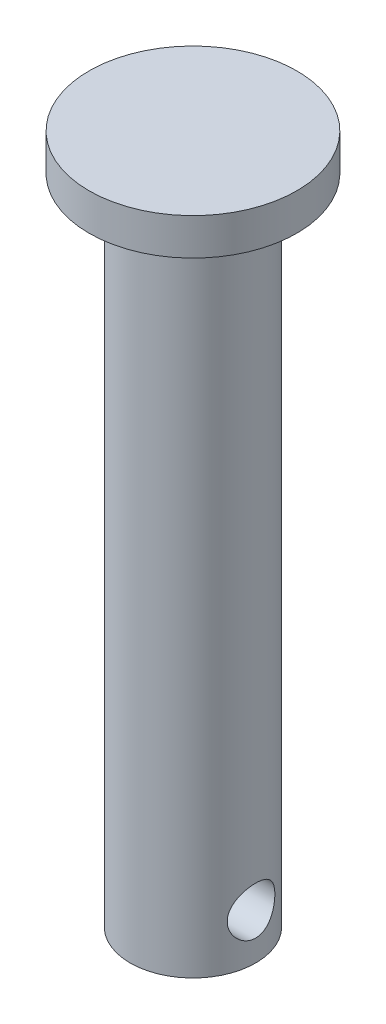
SolidWorks part; units mm, degrees
ref_plane "Front Plane" through (0, 0, 0) normal (0, 0, 1) x (1, 0, 0)
ref_plane "Top Plane" through (0, 0, 0) normal (0, 1, 0) x (1, 0, 0)
ref_plane "Right Plane" through (0, 0, 0) normal (1, 0, 0) x (0, 0, -1)
sketch "Sketch1" plane through (0, 0, 0) normal (0, 1, 0) x (1, 0, 0)
  circle A0 centre (0, 0) radius 2.9
  dimension "D1" = 5.8
extrude "Boss-Extrude1" add sketch "Sketch1" against normal blind 30.15
sketch "Sketch2" plane through (0, 0, 0) normal (0, 1, 0) x (1, 0, 0)
  circle A0 centre (0, 0) radius 4.8
  dimension "D1" = 9.6
extrude "Boss-Extrude2" add sketch "Sketch2" along normal blind 1.7
sketch "Sketch3" plane through (0, 0, 0) normal (1, 0, 0) x (0, 0, -1)
  line L1 (-2.9, -30.15) -> (2.9, -30.15) construction
  circle A0 centre (0, -28.05) radius 1.1
  dimension "D1" = 2.2
  dimension "D2" = 1
extrude "Cut-Extrude1" cut sketch "Sketch3" against normal through all both and the other way through all
